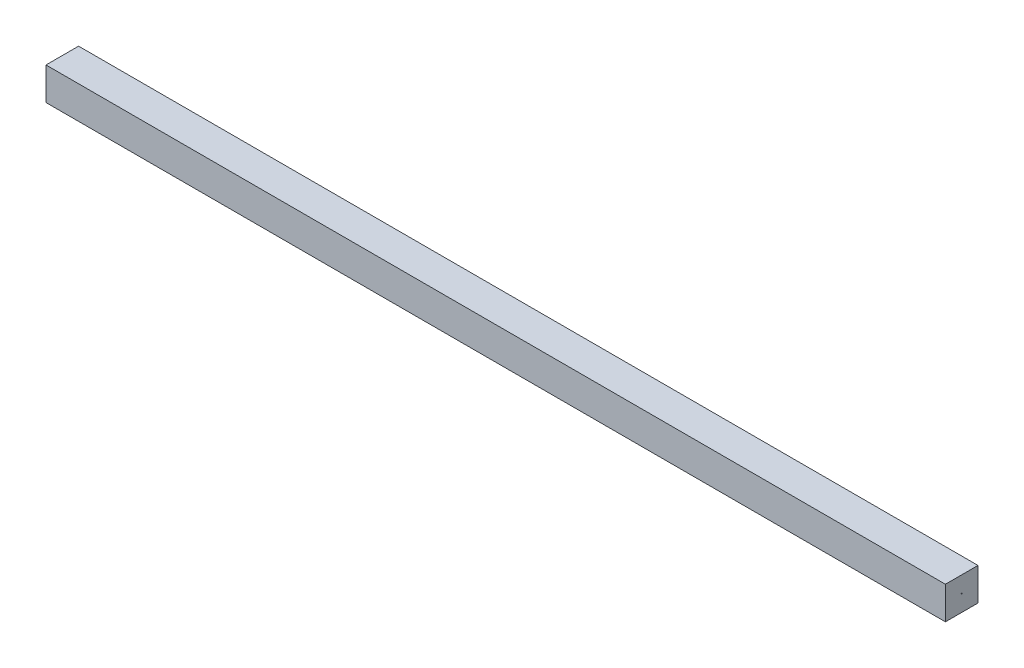
SolidWorks part; units mm, degrees
ref_plane "Front Plane" through (0, 0, 0) normal (0, 0, 1) x (1, 0, 0)
ref_plane "Top Plane" through (0, 0, 0) normal (0, 1, 0) x (1, 0, 0)
ref_plane "Right Plane" through (0, 0, 0) normal (1, 0, 0) x (0, 0, -1)
sketch "Sketch1" plane through (0, 0, 0) normal (1, 0, 0) x (0, 0, -1)
  line L0 (0, 0) -> (30, 0)
  line L1 (30, 0) -> (30, 30)
  line L2 (30, 30) -> (0, 30)
  line L3 (0, 30) -> (0, 0)
  dimension "D1" = 30
  dimension "D2" = 30
extrude "Boss-Extrude2" add sketch "Sketch1" along normal mid plane 828
sketch "Sketch3" plane through (-414, 0, 0) normal (-1, 0, 0) x (0, 0, 1)
  line L0 (0, 30) -> (0, 0) construction
  line L1 (-30, 30) -> (0, 30) construction
  circle A0 centre (-15, 15) radius 0.5
  dimension "D1" = 1
  dimension "D2" = 15
  dimension "D3" = 15
extrude "Boss-Extrude3" add sketch "Sketch3" along normal mid plane 0.5
sketch "Sketch4" plane through (414, 0, 0) normal (1, 0, 0) x (0, 0, -1)
  line L0 (0, 0) -> (30, 0) construction
  line L1 (0, 30) -> (0, 0) construction
  circle A0 centre (15, 15) radius 0.5
  dimension "D1" = 1
  dimension "D2" = 15
  dimension "D3" = 15
extrude "Boss-Extrude4" add sketch "Sketch4" along normal mid plane 0.5
